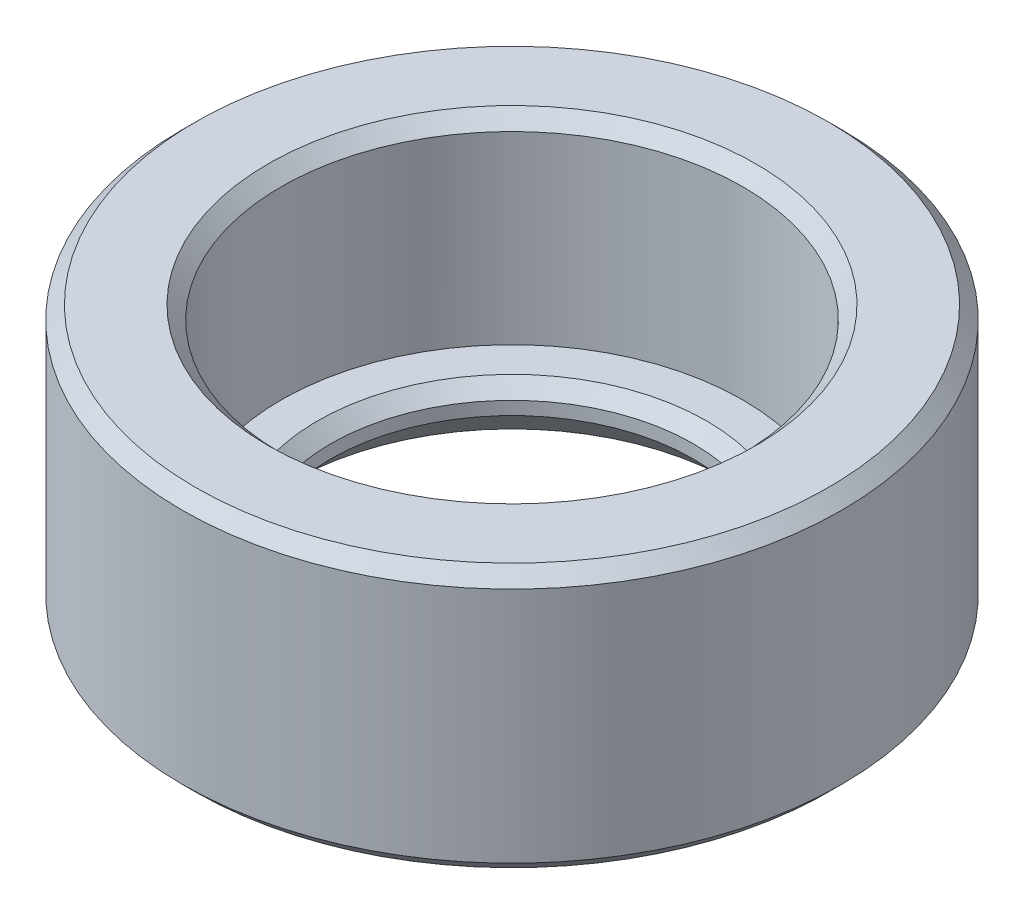
SolidWorks part; units mm, degrees
ref_plane "Front Plane" through (0, 0, 0) normal (0, 0, 1) x (1, 0, 0)
ref_plane "Top Plane" through (0, 0, 0) normal (0, 1, 0) x (1, 0, 0)
ref_plane "Right Plane" through (0, 0, 0) normal (1, 0, 0) x (0, 0, -1)
sketch "Sketch1" plane through (0, 0, 0) normal (0, 1, 0) x (1, 0, 0)
  circle A0 centre (0, 0) radius 5
  circle A1 centre (0, 0) radius 3.5
  dimension "D1" = 7
  dimension "D2" = 10
extrude "Boss-Extrude1" add sketch "Sketch1" along normal blind 4
sketch "Sketch2" plane through (0, 0, 0) normal (0, -1, 0) x (1, 0, 0)
  circle A0 centre (0, 0) radius 2.75
  circle A1 centre (0, 0) radius 5
  dimension "D1" = 5.5
extrude "Boss-Extrude2" add sketch "Sketch2" against normal blind 1
chamfer "Chamfer1" distance 0.2 angle 45 4 edges at (0, 1, -2.75) (0, 0, 5) (0, 4, 5) (0, 4, 3.5)
chamfer "Chamfer2" distance 0.6 angle 45 1 edges at (0, 0, -2.75)
